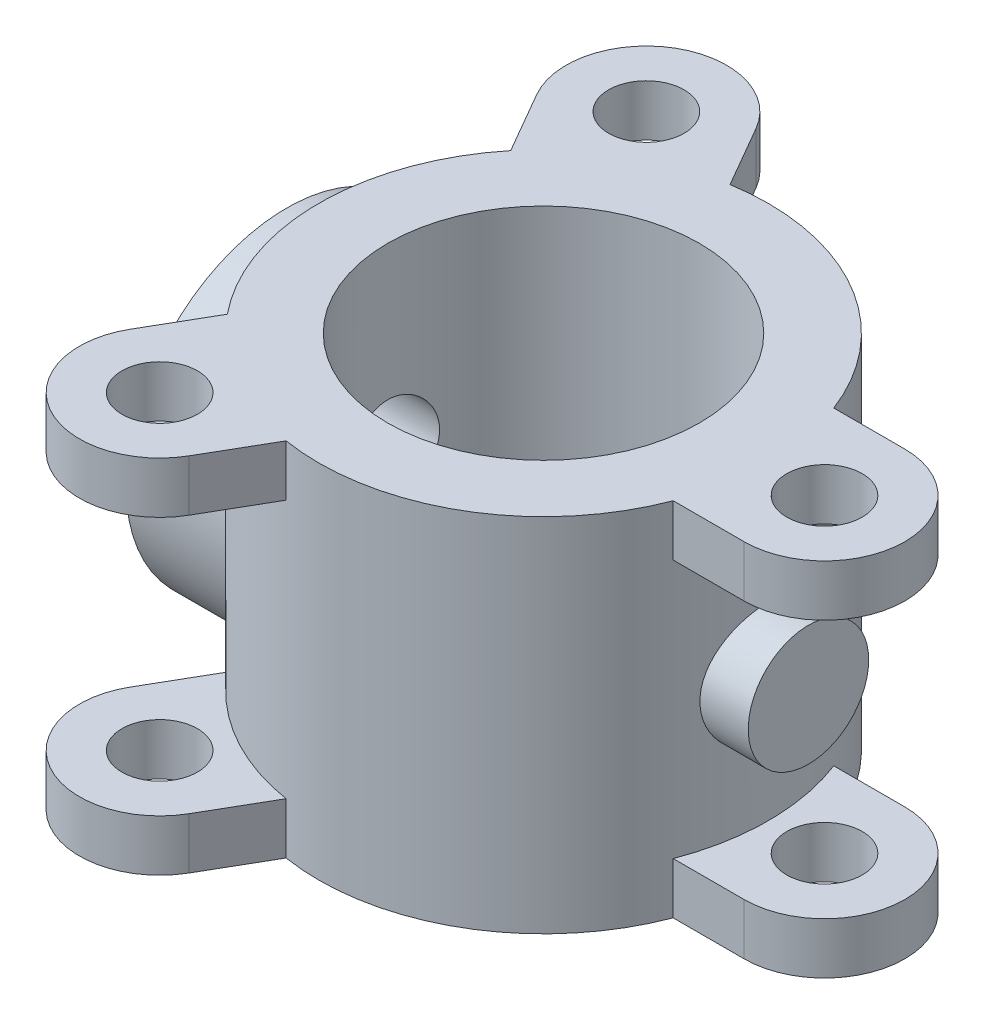
SolidWorks part; units mm, degrees
ref_plane "Front Plane" through (0, 0, 0) normal (0, 0, 1) x (1, 0, 0)
ref_plane "Top Plane" through (0, 0, 0) normal (0, 1, 0) x (1, 0, 0)
ref_plane "Right Plane" through (0, 0, 0) normal (1, 0, 0) x (0, 0, -1)
sketch "Sketch1" plane through (0, 0, 0) normal (0, 1, 0) x (1, 0, 0)
  circle A0 centre (0, 0) radius 97
  circle A1 centre (0, 0) radius 140
  dimension "D1" = 194
  dimension "D2" = 280
extrude "Boss-Extrude1" add sketch "Sketch1" along normal mid plane 225
sketch "Sketch2" plane through (0, 112.5, 0) normal (0, 1, 0) x (1, 0, 0)
  line L0 (175, 50) -> (130.767, 50)
  line L1 (175, -50) -> (130.767, -50)
  circle A0 centre (175, 0) radius 23.5
  arc A1 (175, -50) -> (175, 50) centre (175, 0) ccw
  circle A2 centre (0, 0) radius 140 construction
  circle A3 centre (0, 0) radius 140
  circle M1 centre (0, 0) radius 140
  dimension "D2" = 100
  dimension "D3" = 47
  dimension "D1" = 175
extrude "Boss-Extrude2" add sketch "Sketch2" against normal blind 32 contours L1 A1 L0 A0 M1
pattern_circular "CirPattern1" count 3 over 360 about axis through (0, 0, 0) along (0, 1, 0) of "Boss-Extrude2"
mirror "Mirror1" about plane through (0, 0, 0) normal (0, 1, 0) of "CirPattern1", "Boss-Extrude2"
ref_plane "Plane1" through (-160, 0, 0) normal (1, 0, 0) x (0, 0, -1)
sketch "Sketch3" plane through (-160, 0, 0) normal (1, 0, 0) x (0, 0, -1)
  circle A0 centre (0, 0) radius 28.1
  dimension "D1" = 56.2
extrude "Cut-Extrude1" cut sketch "Sketch3" along normal blind 310
sketch "Sketch4" plane through (-160, 0, 0) normal (1, 0, 0) x (0, 0, -1)
  circle A0 centre (0, 0) radius 100
  dimension "D1" = 200
extrude "Boss-Extrude3" add sketch "Sketch4" along normal up to surface (62.0204 mm away)
sketch "Sketch5" plane through (-160, 0, 0) normal (-1, 0, 0) x (0, 0, 1)
  circle A0 centre (0, 0) radius 50
  dimension "D1" = 100
extrude "Cut-Extrude2" cut sketch "Sketch5" against normal blind 25
sketch "Sketch6" plane through (-160, 0, 0) normal (-1, 0, 0) x (0, 0, 1)
  circle A0 centre (0, 75) radius 10.15
  circle A1 centre (64.9519, -37.5) radius 10.15
  circle A2 centre (-64.9519, -37.5) radius 10.15
  point P9 (0, 0)
  dimension "D1" = 20.3
  dimension "D2" = 75
  dimension "D3" = 3
extrude "Cut-Extrude3" cut sketch "Sketch6" against normal blind 13
ref_plane "Plane2" through (165, 0, 0) normal (1, 0, 0) x (0, 0, -1)
sketch "Sketch7" plane through (165, 0, 0) normal (1, 0, 0) x (0, 0, -1)
  circle A0 centre (0, 0) radius 28.1 construction
  circle A1 centre (0, 0) radius 28.1
  circle A2 centre (0, 0) radius 37.5
  dimension "D1" = 75
extrude "Boss-Extrude4" add sketch "Sketch7" against normal up to next
sketch "Sketch8" plane through (165, 0, 0) normal (1, 0, 0) x (0, 0, -1)
  circle A0 centre (0, 0) radius 37.5 construction
  circle A1 centre (0, 0) radius 37.5
extrude "Boss-Extrude5" add sketch "Sketch8" against normal blind 10
